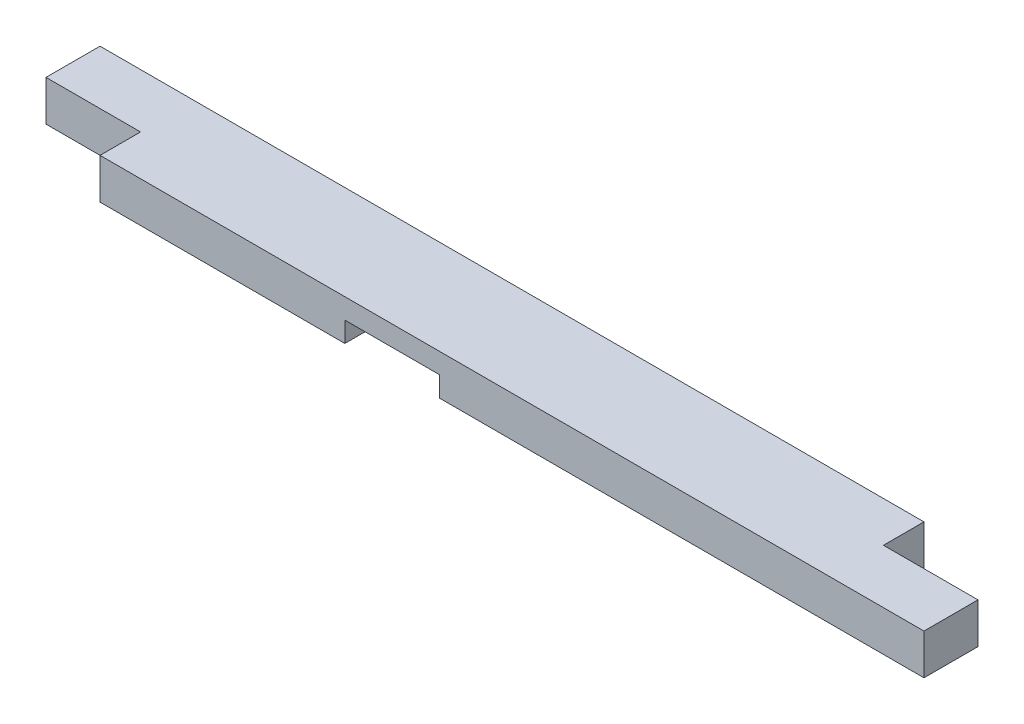
SolidWorks part; units mm, degrees
material "Pine"
ref_plane "Front Plane" through (0, 0, 0) normal (0, 0, 1) x (1, 0, 0)
ref_plane "Top Plane" through (0, 0, 0) normal (0, 1, 0) x (1, 0, 0)
ref_plane "Right Plane" through (0, 0, 0) normal (1, 0, 0) x (0, 0, -1)
sketch "Sketch1" plane through (0, 0, 0) normal (0, 1, 0) x (1, 0, 0)
  line L1 (0, 0) -> (863.6, 0)
  line L2 (0, 0) -> (0, 88.9)
  line L3 (0, 88.9) -> (863.6, 88.9)
  line L4 (863.6, 0) -> (863.6, 88.9)
  dimension "D1" = 88.9
  dimension "D2" = 863.6
extrude "Boss-Extrude1" add sketch "Sketch1" along normal blind 38.1
sketch "Sketch2" plane through (0, 0, 0) normal (0, -1, 0) x (1, 0, 0)
  line L0 (0, 0) -> (863.6, 0) construction
  line L1 (319.0875, 0) -> (407.9875, 0)
  line L2 (319.0875, 0) -> (319.0875, -88.9)
  line L3 (319.0875, -88.9) -> (407.9875, -88.9)
  line L4 (407.9875, 0) -> (407.9875, -88.9)
  line L5 (863.6, -88.9) -> (0, -88.9) construction
  dimension "D1" = 319.0875
  dimension "D2" = 88.9
extrude "Cut-Extrude1" cut sketch "Sketch2" against normal blind 19.05
sketch "Sketch3" plane through (0, 38.1, 0) normal (0, 1, 0) x (1, 0, 0)
  line L1 (0, 0) -> (88.9, 0)
  line L2 (0, 0) -> (0, 38.1)
  line L3 (0, 38.1) -> (88.9, 38.1)
  line L4 (88.9, 0) -> (88.9, 38.1)
  dimension "D1" = 88.9
  dimension "D2" = 38.1
extrude "Cut-Extrude2" cut sketch "Sketch3" against normal through all
sketch "Sketch4" plane through (0, 38.1, 0) normal (0, 1, 0) x (1, 0, 0)
  line L0 (863.6, 88.9) -> (0, 88.9) construction
  line L1 (774.7, 88.9) -> (863.6, 88.9)
  line L2 (774.7, 88.9) -> (774.7, 50.8)
  line L3 (774.7, 50.8) -> (863.6, 50.8)
  line L4 (863.6, 88.9) -> (863.6, 50.8)
  line L5 (863.6, 0) -> (863.6, 88.9) construction
  dimension "D1" = 774.7
  dimension "D2" = 50.8
extrude "Cut-Extrude3" cut sketch "Sketch4" against normal through all
